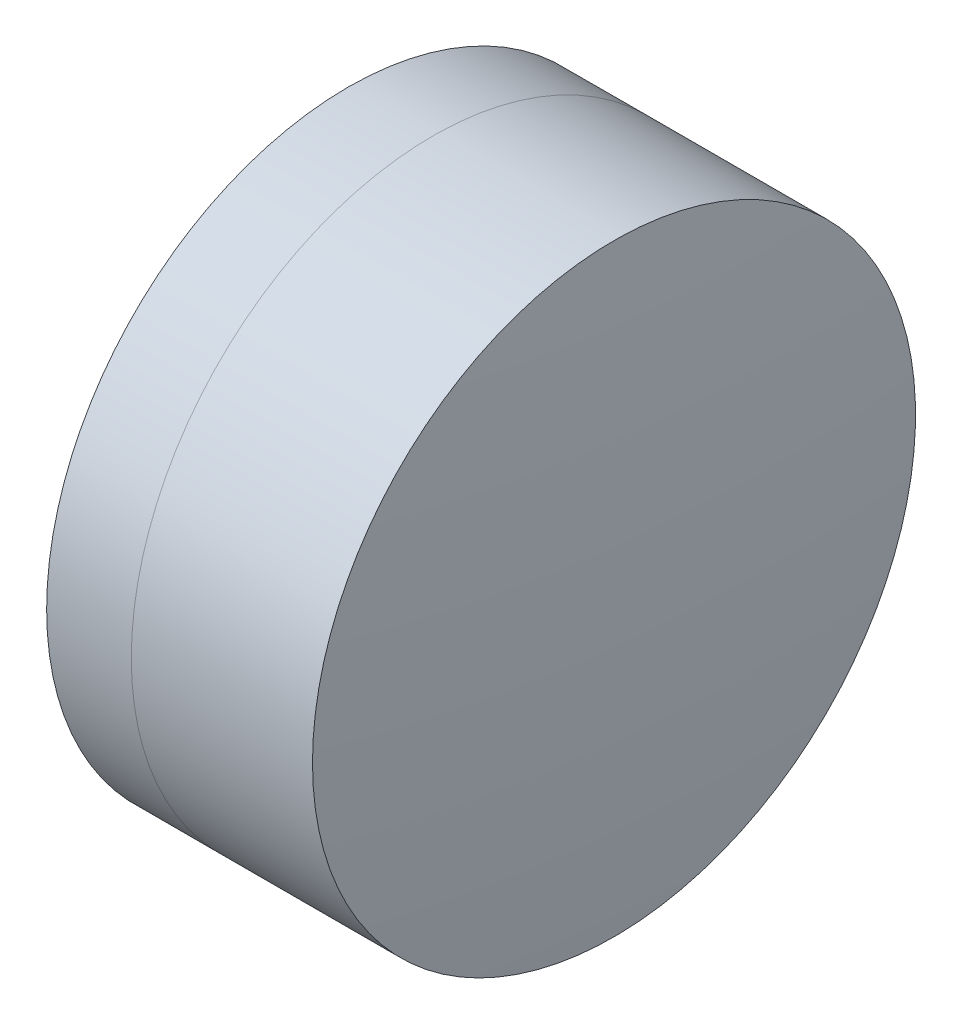
SolidWorks part; units mm, degrees
ref_plane "前视基准面" through (0, 0, 0) normal (0, 0, 1) x (1, 0, 0)
ref_plane "上视基准面" through (0, 0, 0) normal (0, 1, 0) x (1, 0, 0)
ref_plane "右视基准面" through (0, 0, 0) normal (1, 0, 0) x (0, 0, -1)
sketch "草图1" plane through (0, 0, 0) normal (0, 1, 0) x (1, 0, 0)
  line L0 (-9.7026, 0) -> (11.7646, 0) construction
  line L1 (-2.4173, -6.35) -> (-0.6347, -6.35)
  line L2 (-2.4173, 6.35) -> (-0.6347, 6.35)
  arc A0 (-0.6347, -6.35) -> (-0.6347, 6.35) centre (-9.1222, 0) ccw
  arc A1 (-2.4173, 6.35) -> (-2.4173, -6.35) centre (15.2778, 0) ccw
  point P10 (-3.5222, 0)
  point P11 (1.4778, 0)
  dimension "D3" = 18.8
  dimension "D4" = 10.6
  dimension "D1" = 6.35
  dimension "D2" = 6.35
  dimension "D5" = 5
revolve "旋转1" add sketch "草图1" angle 360 about L0
sketch "草图2" plane through (0, 0, 0) normal (0, 1, 0) x (1, 0, 0)
  line L0 (-0.5519, 0) -> (13.3053, 0) construction
  line L2 (-0.6347, 6.35) -> (3.1811, 6.35)
  line L3 (-0.6347, -6.35) -> (3.1811, -6.35)
  arc A0 (3.1811, -6.35) -> (3.1811, 6.35) centre (-64.6222, 0) ccw
  arc A1 (-0.6347, -6.35) -> (-0.6347, 6.35) centre (-9.1222, 0) ccw construction
  arc A2 (-0.6347, -6.35) -> (-0.6347, 6.35) centre (-9.1222, 0) ccw
  point P4 (1.4778, 0)
  point P8 (3.4778, 0)
  dimension "D1" = 68.1
  dimension "D2" = 2
revolve "旋转3" add sketch "草图2" angle 360 about L0
